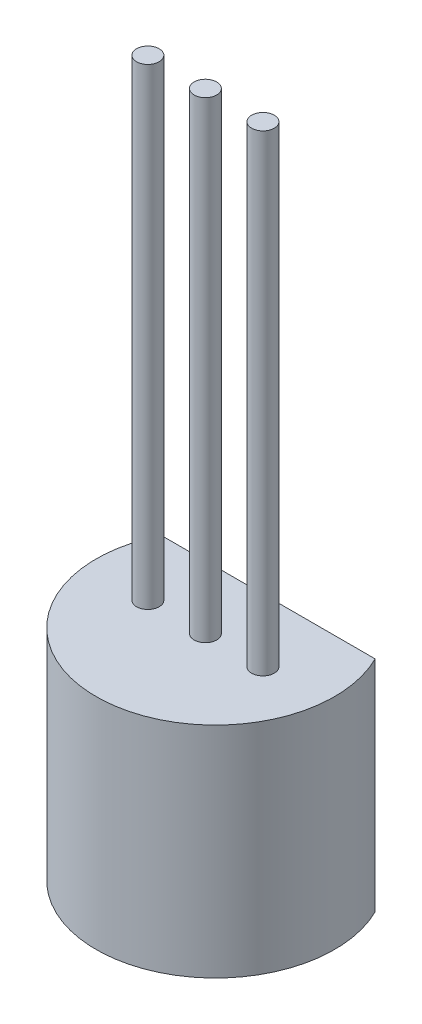
SolidWorks part; units mm, degrees
ref_plane "Front Plane" through (0, 0, 0) normal (0, 0, 1) x (1, 0, 0)
ref_plane "Top Plane" through (0, 0, 0) normal (0, 1, 0) x (1, 0, 0)
ref_plane "Right Plane" through (0, 0, 0) normal (1, 0, 0) x (0, 0, -1)
sketch "Sketch1" plane through (0, 0, 0) normal (0, 1, 0) x (1, 0, 0)
  line L0 (-2.6, 0) -> (2.6, 0)
  arc A0 (2.6, 0) -> (-2.6, 0) centre (0, -1.2883) cw
  point P2 (0, 0)
  dimension "D1" = 5.2
extrude "Boss-Extrude1" add sketch "Sketch1" along normal blind 5.33
sketch "Sketch2" plane through (0, 5.33, 0) normal (0, 1, 0) x (1, 0, 0)
  line L0 (-2.6, 0) -> (2.6, 0)
  line L1 (-2.6, -1.53) -> (2.6, -1.53) construction
  line L2 (0, 1.0444) -> (0, -6.1171) construction
  circle A0 centre (0, -1.53) radius 0.275
  circle A1 centre (1.4, -1.53) radius 0.275
  circle A2 centre (-1.4, -1.53) radius 0.275
  dimension "D2" = 2
  dimension "D1" = 1.53
extrude "Boss-Extrude2" add sketch "Sketch2" along normal blind 11.4843 contours A0 | A2 | A1
